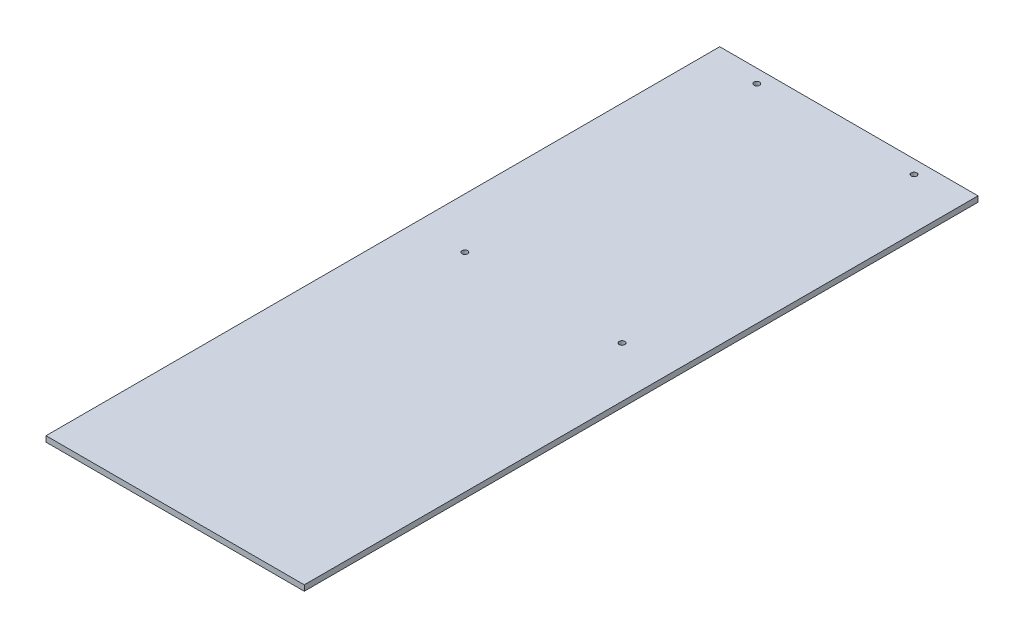
SolidWorks part; units mm, degrees
material "Mahogany"
ref_plane "Front Plane" through (0, 0, 0) normal (0, 0, 1) x (1, 0, 0)
ref_plane "Top Plane" through (0, 0, 0) normal (0, 1, 0) x (1, 0, 0)
ref_plane "Right Plane" through (0, 0, 0) normal (1, 0, 0) x (0, 0, -1)
sketch "Sketch1" plane through (0, 0, 0) normal (0, 1, 0) x (1, 0, 0)
  line L1 (0, 0) -> (230, 0)
  line L2 (0, 0) -> (0, 600)
  line L3 (0, 600) -> (230, 600)
  line L4 (230, 0) -> (230, 600)
extrude "Boss-Extrude1" add sketch "Sketch1" along normal blind 5
sketch "Sketch2" plane through (0, 5, 0) normal (0, 1, 0) x (1, 0, 0)
  line L0 (115, 600) -> (115, 0) construction
  line L1 (230, 600) -> (0, 600) construction
  line L2 (0, 0) -> (230, 0) construction
  circle A0 centre (185.01, 588) radius 2.5
  circle A1 centre (44.99, 588) radius 2.5
  circle A2 centre (185, 328) radius 2.5
  circle A3 centre (45, 328) radius 2.5
  dimension "D1" = 70.01
  dimension "D5" = 140
  dimension "D2" = 70.01
  dimension "D3" = 12
  dimension "D4" = 12
  dimension "D6" = 70
  dimension "D7" = 260
  dimension "D8" = 260
extrude "Cut-Extrude1" cut sketch "Sketch2" against normal blind 10
